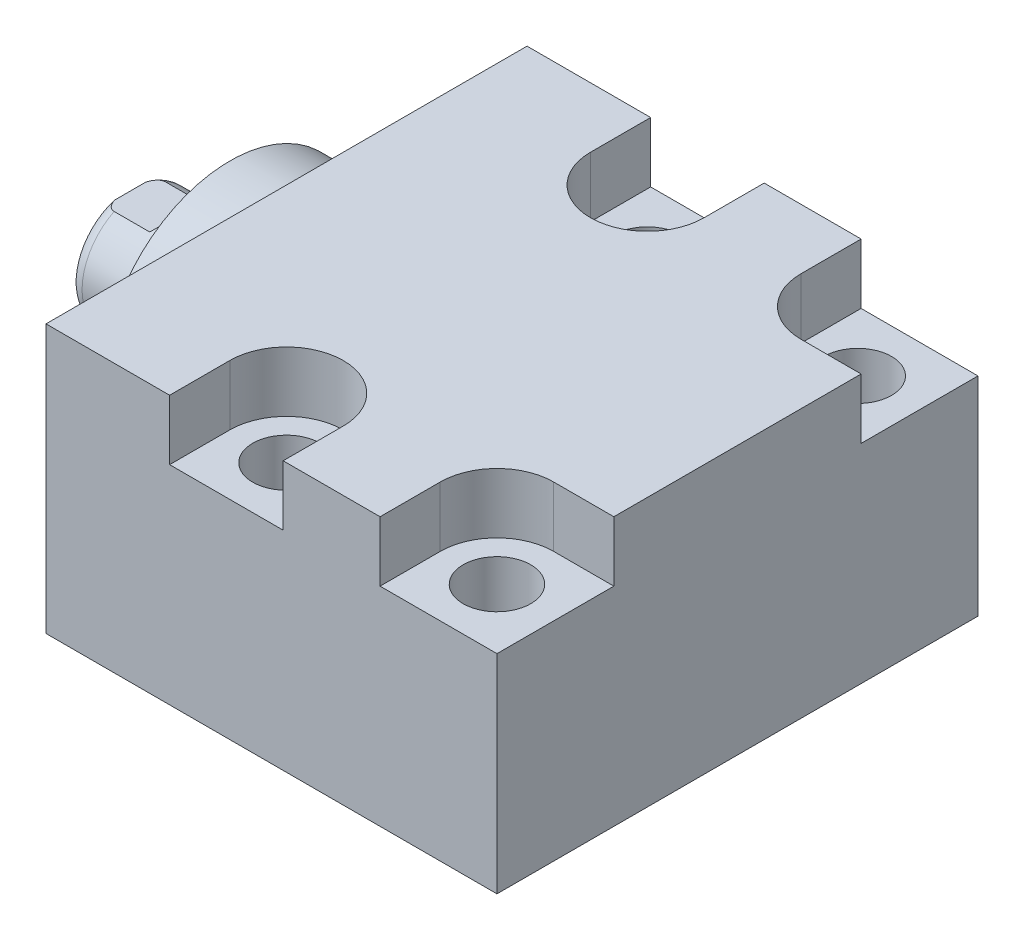
SolidWorks part; units mm, degrees
material "Alloy Steel"
ref_plane "Front Plane" through (0, 0, 0) normal (0, 0, 1) x (1, 0, 0)
ref_plane "Top Plane" through (0, 0, 0) normal (0, 1, 0) x (1, 0, 0)
ref_plane "Right Plane" through (0, 0, 0) normal (1, 0, 0) x (0, 0, -1)
ref_plane "Plane1" through (0, 0, 0) normal (1, 0, 0) x (0, 0, -1)
sketch "Sketch1" plane through (0, 0, 0) normal (1, 0, 0) x (0, 0, -1)
  line L0 (-25.4, 14.2748) -> (25.4, 14.2748)
  line L1 (25.4, 14.2748) -> (25.4, -14.0462)
  line L2 (25.4, -14.0462) -> (-25.4, -14.0462)
  line L3 (-25.4, -14.0462) -> (-25.4, 14.2748)
  line L4 (0, -24.4475) -> (0, 24.4475) construction
  dimension "D1" = 28.321
  dimension "D2" = 14.0462
  dimension "D3" = 50.8
  dimension "D4" = 25.4
extrude "Extrude1" add sketch "Sketch1" along normal blind 47.625
sketch "Sketch5" plane through (0, 0, 0) normal (-1, 0, 0) x (0, 0, 1)
  circle A0 centre (0, 0) radius 13.5001
  dimension "D1" = 27.0002
extrude "Extrude2" add sketch "Sketch5" along normal blind 5.969
ref_plane "Plane5" through (0, 0, 0) normal (0, -1, 0) x (0, 0, 1)
sketch "Sketch6" plane through (0, 0, 0) normal (0, -1, 0) x (0, 0, 1)
  line L0 (0, 5.969) -> (-6.35, 5.969)
  line L1 (-6.35, 5.969) -> (-6.35, 16.51)
  line L2 (-6.35, 16.51) -> (0, 16.51)
  line L3 (0, 16.51) -> (0, 5.969)
  line L4 (0, -5.7546) -> (0, 21.1709) construction
  line L5 (13.5001, 5.969) -> (-13.5001, 5.969) construction
  line L6 (25.4, -47.625) -> (-25.4, -47.625) construction
  dimension "D1" = 64.135
  dimension "D2" = 12.7
revolve "Revolve1" add sketch "Sketch6" angle 360 about L4
ref_plane "Plane6" through (-18.5113, 3.2639, 0) normal (0, 0, 1) x (0, 1, 0)
sketch "S2D0001" plane through (-18.5113, 3.2639, 0) normal (0, 0, 1) x (0, 1, 0)
  line L0 (-0.7112, -3.5631) -> (-0.7112, -18.0033)
  line L1 (-3.2639, -19.5371) -> (-0.7112, -18.0033)
  line L2 (0.1905, -2.0013) -> (-3.2639, -2.0013)
  line L3 (-3.2639, -2.0013) -> (-3.2639, -19.5371)
  line L4 (-0.7112, -3.5631) -> (0.1905, -2.0013)
  line L5 (-3.2639, -18.5113) -> (-3.2639, 2.765) construction
  line L6 (3.0861, -2.0013) -> (-9.6139, -2.0013) construction
  dimension "D1" = 30
  dimension "D2" = 6.9088
  dimension "D3" = 5.1054
  dimension "D4" = 16.002
  dimension "D5" = 59
revolve "Cut-Revolve4" cut sketch "S2D0001" angle 360 about L5
ref_plane "Plane7" through (0, 0, 0) normal (0, 1, 0) x (0, 0, -1)
sketch "Sketch8" plane through (0, 0, 0) normal (0, 1, 0) x (0, 0, -1)
  line L0 (-6.35, 10.1854) -> (-6.096, 10.9474)
  line L1 (-6.096, 10.9474) -> (-6.096, 15.494)
  line L2 (0, 12.6594) -> (0, 20.8178) construction
  line L3 (-6.35, 10.1854) -> (-6.35, 16.51)
  line L4 (-5.7079, 16.51) -> (-6.35, 16.51)
  line L5 (6.35, 16.51) -> (-6.35, 16.51) construction
  line L6 (-6.35, 16.51) -> (-6.35, 5.969) construction
  arc A0 (-5.7079, 16.51) -> (-6.096, 15.494) centre (-4.572, 15.494) ccw
  dimension "D2" = 1.524
  dimension "D1" = 12.192
  dimension "D3" = 1.016
  dimension "D4" = 0.762
  dimension "D5" = 5.5626
revolve "Cut-Revolve5" cut sketch "Sketch8" angle 360 about L2
ref_plane "Plane11" through (0, 0, 0) normal (0, 0, -1) x (0, -1, 0)
sketch "Sketch12" plane through (0, 0, 0) normal (0, 0, -1) x (0, -1, 0)
  line L0 (5.461, 16.51) -> (5.461, 11.7348)
  line L1 (5.461, 11.7348) -> (6.096, 11.0998)
  line L2 (-5.461, 16.51) -> (-5.461, 11.7348)
  line L3 (-5.461, 11.7348) -> (-6.096, 11.0998)
  line L4 (5.461, 16.51) -> (6.096, 16.51)
  line L5 (0, 13.7262) -> (0, 20.767) construction
  line L6 (-6.096, 11.0998) -> (-6.096, 16.51)
  line L8 (6.096, 10.9474) -> (6.096, 15.494) construction
  line L9 (6.096, 11.0998) -> (6.096, 16.51)
  line L10 (-5.461, 16.51) -> (-6.096, 16.51)
  line L12 (5.7079, 16.51) -> (-5.7079, 16.51) construction
  dimension "D1" = 10.922
  dimension "D2" = 4.7752
  dimension "D3" = 45
extrude "Cut-Extrude4" cut sketch "Sketch12" against normal mid plane 60.96
hole_wizard "Hole2" positions "Sketch17" profile "Sketch16" legacy
sketch "Sketch17" plane through (0, 14.2748, 0) normal (0, 1, 0) x (-1, 0, 0)
  line L0 (0, 0) -> (-59.3363, 0) construction
  line L1 (0, -25.4) -> (0, 25.4) construction
  point P0 (-19.05, -19.05)
  point P9 (-19.05, 19.05)
  dimension "D1" = 38.1
  dimension "D2" = 19.05
sketch "Sketch16" plane through (19.05, 14.2748, -19.05) normal (1, 0, 0) x (0, 0, 1)
  line L0 (0, 0) -> (0, 28.321)
  line L1 (0, 28.321) -> (3.5687, 28.321)
  line L2 (3.5687, 28.321) -> (3.5687, 0)
  line L3 (3.5687, 0) -> (0, 0)
  line L4 (0, 110) -> (0, -10) construction
  dimension "Diameter" = 7.1374
  dimension "Depth" = 28.321
pattern_linear "LPattern1" count 2 spacing 22.225 along (1, 0, 0) of "Hole2"
sketch "Sketch18" plane through (0, 14.2748, 0) normal (0, 1, 0) x (1, 0, 0)
  line L0 (0, 0) -> (50.053, 0) construction
  line L2 (47.625, -25.4) -> (0, -25.4) construction
  line L3 (47.625, 25.4) -> (47.625, -25.4) construction
  line L4 (47.625, -25.4) -> (35.2806, -25.4)
  line L5 (13.0556, -19.05) -> (13.0556, -25.4)
  line L6 (25.0444, -19.05) -> (25.0444, -25.4)
  line L7 (35.2806, -19.05) -> (35.2806, -25.4)
  line L8 (41.275, -13.0556) -> (47.625, -13.0556)
  line L9 (25.0444, -25.4) -> (13.0556, -25.4)
  line L10 (47.625, -13.0556) -> (47.625, -25.4)
  line L11 (47.625, 13.0556) -> (47.625, 25.4)
  line L12 (25.0444, 25.4) -> (13.0556, 25.4)
  line L13 (41.275, 13.0556) -> (47.625, 13.0556)
  line L14 (35.2806, 19.05) -> (35.2806, 25.4)
  line L15 (25.0444, 19.05) -> (25.0444, 25.4)
  line L16 (13.0556, 19.05) -> (13.0556, 25.4)
  line L17 (47.625, 25.4) -> (35.2806, 25.4)
  arc A0 (25.0444, -19.05) -> (13.0556, -19.05) centre (19.05, -19.05) ccw
  arc A1 (41.275, -13.0556) -> (35.2806, -19.05) centre (41.275, -19.05) ccw
  arc A2 (41.275, 13.0556) -> (35.2806, 19.05) centre (41.275, 19.05) cw
  arc A3 (25.0444, 19.05) -> (13.0556, 19.05) centre (19.05, 19.05) cw
  dimension "D1" = 11.9888
extrude "Cut-Extrude5" cut sketch "Sketch18" against normal blind 6.35
hole_wizard "Hole3" positions "Sketch20" profile "Sketch19" legacy
sketch "Sketch20" plane through (0, -14.0462, 0) normal (0, -1, 0) x (1, 0, 0)
  line L0 (0, 25.4) -> (0, -25.4) construction
  point P0 (12.7, 0)
  dimension "D1" = 12.7
sketch "Sketch19" plane through (12.7, -14.0462, 0) normal (1, 0, 0) x (0, 0, -1)
  line L0 (0, 0) -> (0, 14.9413)
  line L1 (0, 14.9413) -> (1.1938, 14.224)
  line L2 (1.1938, 14.224) -> (1.1938, 1.4478)
  line L3 (1.1938, 1.4478) -> (5.6705, 1.4478)
  line L4 (5.6705, 0) -> (0, 0)
  line L5 (0, -11.3109) -> (0, 121.1557) construction
  line L6 (0, 14.9413) -> (-1.1938, 14.224) construction
  line L7 (5.6705, 1.4478) -> (5.6705, 0)
  dimension "Depth" = 14.224
  dimension "Drill Angle" = 118
  dimension "Diameter" = 2.3876
  dimension "C-Bore Diameter" = 11.3411
  dimension "C-Bore Depth" = 1.4478
hole_wizard "Hole4" positions "Sketch21" profile "Sketch22" legacy
sketch "Sketch21" plane through (0, -14.0462, 0) normal (0, -1, 0) x (1, 0, 0)
  point P0 (36.3474, 0)
  dimension "D1" = 23.6474
sketch "Sketch22" plane through (36.3474, -14.0462, 0) normal (1, 0, 0) x (0, 0, -1)
  line L0 (0, 0) -> (0, 15.1779)
  line L1 (0, 15.1779) -> (1.5875, 14.224)
  line L2 (1.5875, 14.224) -> (1.5875, 0)
  line L4 (1.5875, 0) -> (0, 0)
  line L5 (0, -11.3109) -> (0, 121.1557) construction
  line L6 (0, 15.1779) -> (-1.5875, 14.224) construction
  dimension "Depth" = 14.224
  dimension "Drill Angle" = 118
  dimension "Diameter" = 3.175
sketch "Sketch26" plane through (0, -14.0462, 0) normal (0, -1, 0) x (1, 0, 0)
  circle A0 centre (34.925, 0) radius 5.6769
  dimension "D2" = 11.3538
  dimension "D1" = 22.225
extrude "Cut-Extrude6" cut sketch "Sketch26" against normal blind 1.4478
chamfer "Chamfer1" distance 0.635 angle 45 2 edges at (12.7, -12.5984, -1.1938) (36.3474, -12.5984, -1.5875)
sketch "Sketch23" plane through (0, 0, 0) normal (0, 0, 1) x (1, 0, 0)
  line L0 (12.7, -12.5984) -> (12.7, -21.4272) construction
  line L1 (10.8712, -12.5984) -> (14.5288, -12.5984) construction
  line L2 (7.0294, -12.5984) -> (18.3705, -12.5984) construction
  line L3 (7.0294, -12.5984) -> (7.0294, -14.0462) construction
  circle A0 centre (8.4772, -14.0462) radius 1.4478
  dimension "D1" = 2.8956
revolve "Revolve2" add sketch "Sketch23" angle 360 about L0
pattern_linear "LPattern3" count 2 spacing 22.225 along (1, 0, 0) of bodies 128
